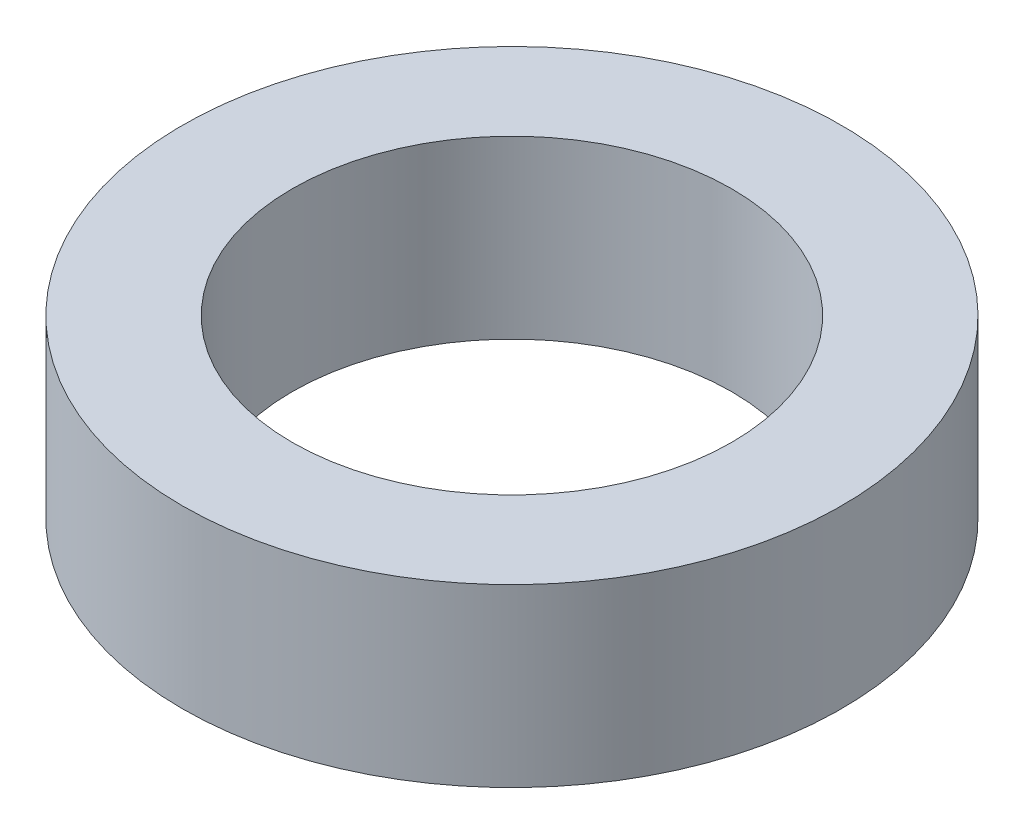
SolidWorks part; units mm, degrees
ref_plane "前视基准面" through (0, 0, 0) normal (0, 0, 1) x (1, 0, 0)
ref_plane "上视基准面" through (0, 0, 0) normal (0, 1, 0) x (1, 0, 0)
ref_plane "右视基准面" through (0, 0, 0) normal (1, 0, 0) x (0, 0, -1)
sketch "草图1" plane through (0, 0, 0) normal (0, 1, 0) x (1, 0, 0)
  circle A0 centre (0, 0) radius 2
  circle A1 centre (0, 0) radius 3
  dimension "D1" = 4
  dimension "D2" = 6
extrude "凸台-拉伸1" add sketch "草图1" along normal blind 1.6
